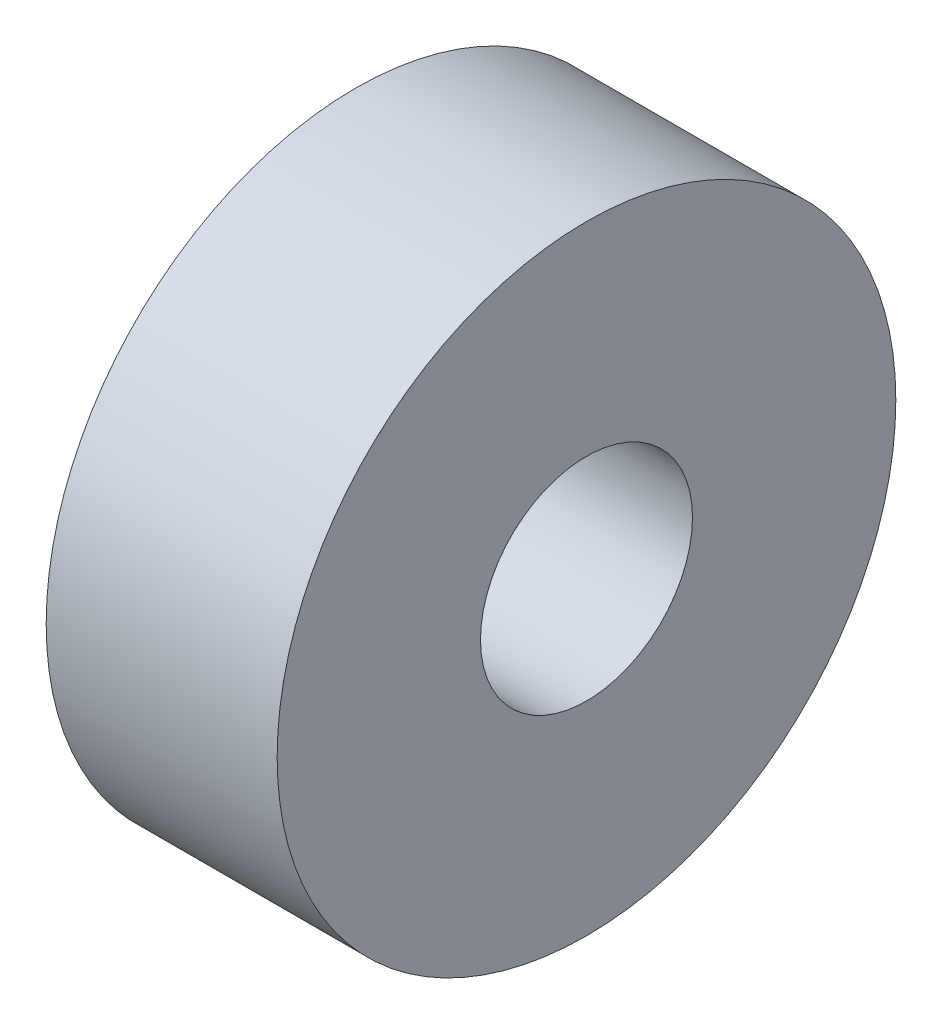
SolidWorks part; units mm, degrees
material "Plain Carbon Steel"
ref_plane "Front Plane" through (0, 0, 0) normal (0, 0, 1) x (1, 0, 0)
ref_plane "Top Plane" through (0, 0, 0) normal (0, 1, 0) x (1, 0, 0)
ref_plane "Right Plane" through (0, 0, 0) normal (1, 0, 0) x (0, 0, -1)
sketch "Sketch2" plane through (0, 0, 0) normal (1, 0, 0) x (0, 0, -1)
  circle A0 centre (0, 0) radius 3.2639
  circle A1 centre (0, 0) radius 9.525
  dimension "D1" = 6.5278
  dimension "D2" = 19.05
extrude "Boss-Extrude1" add sketch "Sketch2" along normal blind 7.112
